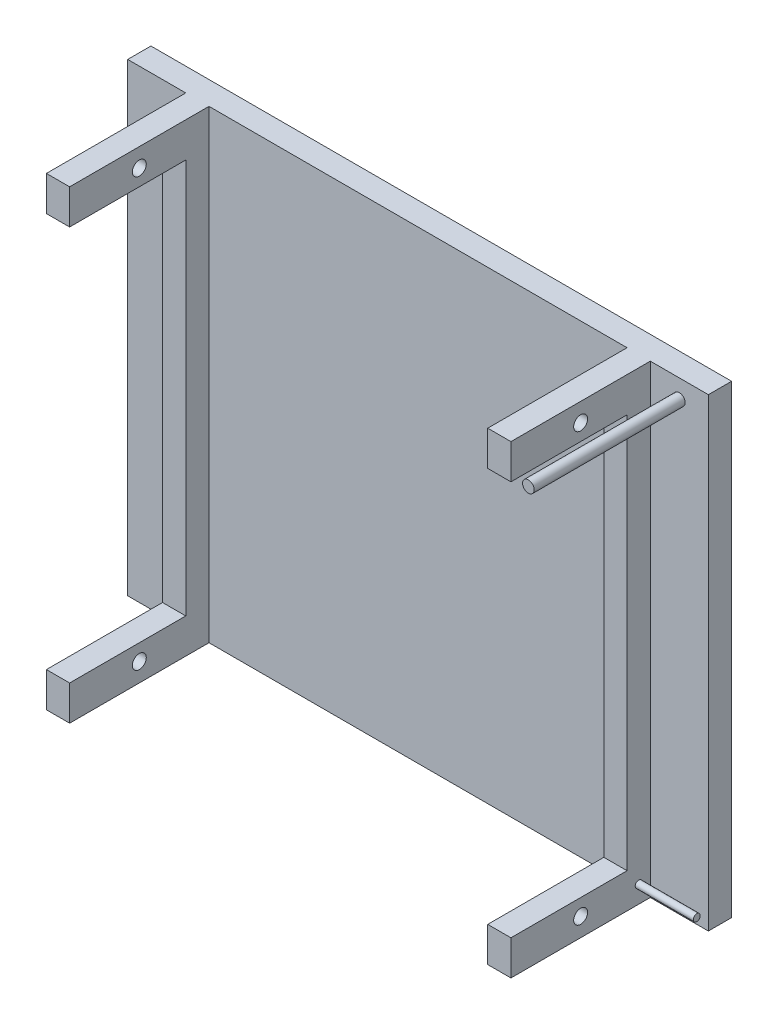
SolidWorks part; units mm, degrees
ref_plane "Plan de face" through (0, 0, 0) normal (0, 0, 1) x (1, 0, 0)
ref_plane "Plan de dessus" through (0, 0, 0) normal (0, 1, 0) x (1, 0, 0)
ref_plane "Plan de droite" through (0, 0, 0) normal (1, 0, 0) x (0, 0, -1)
sketch "Esquisse1" plane through (0, 0, 0) normal (0, 0, 1) x (1, 0, 0)
  line L1 (0, 0) -> (250, 0)
  line L2 (0, 0) -> (0, -200)
  line L3 (0, -200) -> (250, -200)
  line L4 (250, 0) -> (250, -200)
  dimension "D1" = 200
  dimension "D2" = 250
extrude "Boss.-Extru.1" add sketch "Esquisse1" along normal blind 10
sketch "Esquisse2" plane through (0, 0, 10) normal (0, 0, 1) x (1, 0, 0)
  line L0 (250, 0) -> (0, 0) construction
  line L1 (25, 0) -> (35, 0)
  line L2 (25, 0) -> (25, -200)
  line L3 (25, -200) -> (35, -200)
  line L4 (35, 0) -> (35, -200)
  line L5 (0, -200) -> (250, -200) construction
  line L6 (0, 0) -> (0, -200) construction
  line L7 (225, 0) -> (215, 0)
  line L8 (225, 0) -> (225, -200)
  line L9 (225, -200) -> (215, -200)
  line L10 (215, 0) -> (215, -200)
  line L11 (250, -200) -> (250, 0) construction
  dimension "D1" = 25
  dimension "D2" = 25
  dimension "D3" = 10
  dimension "D4" = 10
extrude "Boss.-Extru.2" add sketch "Esquisse2" along normal blind 60
sketch "Esquisse3" plane through (225, 0, 0) normal (1, 0, 0) x (0, 0, -1)
  line L0 (-70, -200) -> (-70, 0) construction
  line L1 (-70, -15) -> (-20, -15)
  line L2 (-70, -15) -> (-70, -185)
  line L3 (-70, -185) -> (-20, -185)
  line L4 (-20, -15) -> (-20, -185)
  line L5 (-70, 0) -> (-10, 0) construction
  line L6 (-70, -200) -> (-10, -200) construction
  line L7 (-10, -200) -> (-10, 0) construction
  circle A0 centre (-40, -192) radius 3
  circle A1 centre (-40, -8) radius 3
  dimension "D4" = 6
  dimension "D5" = 6
  dimension "D1" = 15
  dimension "D2" = 15
  dimension "D3" = 10
  dimension "D6" = 8
  dimension "D7" = 8
  dimension "D8" = 30
extrude "Enlèv. mat.-Extru.1" cut sketch "Esquisse3" against normal through all
sketch "Esquisse4" plane through (0, 0, 10) normal (0, 0, 1) x (1, 0, 0)
  line L0 (250, -200) -> (250, 0) construction
  line L1 (250, 0) -> (225, 0) construction
  circle A0 centre (237.5, -8) radius 2.5
  dimension "D1" = 5
  dimension "D2" = 12.5
  dimension "D3" = 8
extrude "Boss.-Extru.5" add sketch "Esquisse4" along normal blind 65
sketch "Esquisse5" plane through (225, 0, 0) normal (1, 0, 0) x (0, 0, -1)
  line L0 (-10, -200) -> (-10, 0) construction
  line L1 (-70, 0) -> (-10, 0) construction
  circle A0 centre (-15, -83) radius 1.5
  dimension "D1" = 3
  dimension "D2" = 5
  dimension "D3" = 83
sketch "Esquisse8" plane through (225, 0, 0) normal (1, 0, 0) x (0, 0, -1)
  line L0 (-70, -200) -> (-10, -200) construction
  line L1 (-10, -200) -> (-10, 0) construction
  circle A1 centre (-15, -192.5) radius 1.5
  point P2 (0, 0)
  point P3 (0, 0)
  dimension "D3" = 3
  dimension "D1" = 7.5
  dimension "D2" = 5
extrude "Boss.-Extru.8" add sketch "Esquisse8" along normal blind 25
